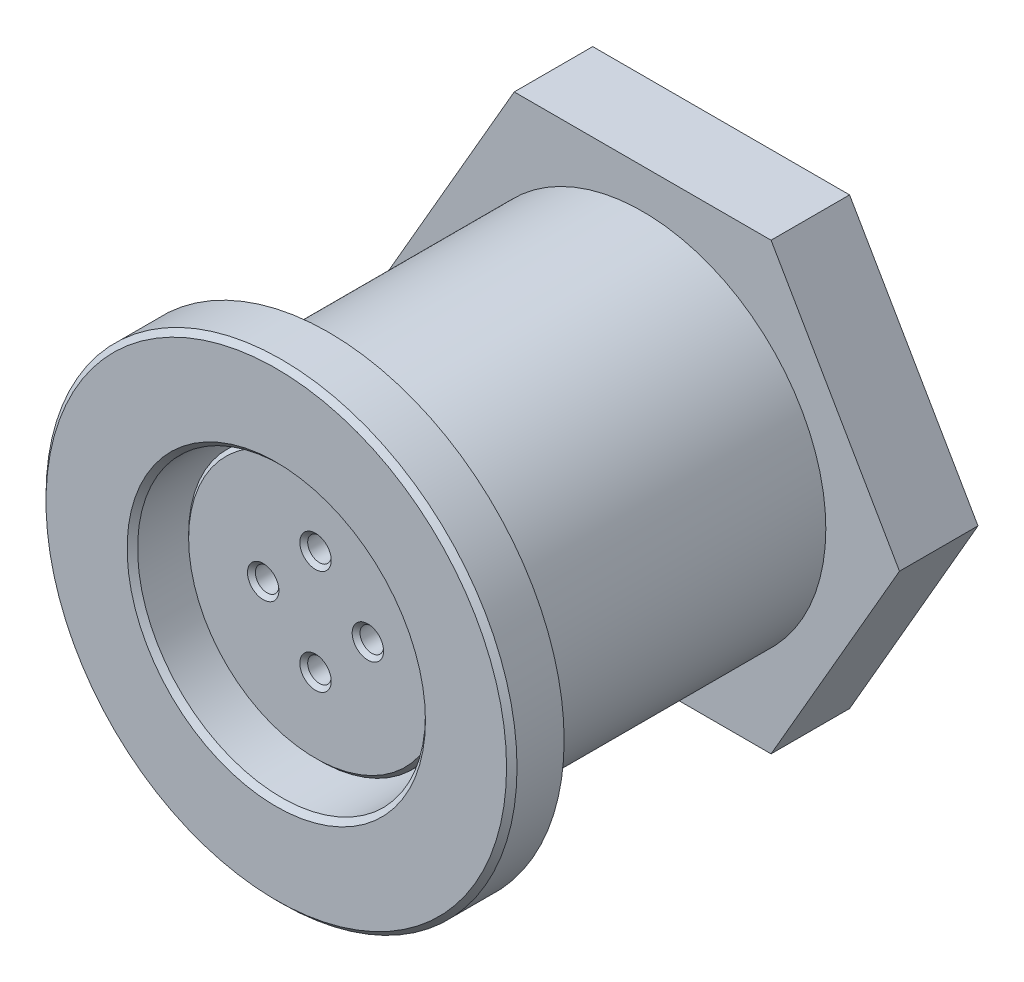
SolidWorks part; units mm, degrees
material "1060 Alloy"
ref_plane "Front Plane" through (0, 0, 0) normal (0, 0, 1) x (1, 0, 0)
ref_plane "Top Plane" through (0, 0, 0) normal (0, 1, 0) x (1, 0, 0)
ref_plane "Right Plane" through (0, 0, 0) normal (1, 0, 0) x (0, 0, -1)
sketch "Sketch1" plane through (0, 0, 0) normal (0, 0, 1) x (1, 0, 0)
  circle A0 centre (0, 0) radius 9
extrude "Extrude1" add sketch "Sketch1" along normal blind 2
sketch "Sketch3" plane through (0, 0, 0) normal (0, 0, -1) x (-1, 0, 0)
  circle A0 centre (0, 0) radius 8.25
  circle A1 centre (0, 0) radius 7
sketch "Sketch4" plane through (0, 0, 0) normal (0, 0, -1) x (-1, 0, 0)
  circle A0 centre (0, 0) radius 7
extrude "Extrude2" add sketch "Sketch4" along normal blind 16
sketch "Sketch2" plane through (0, 0, 2) normal (0, 0, 1) x (1, 0, 0)
  circle A0 centre (0, 0) radius 5.5
extrude "Cut-Extrude1" cut sketch "Sketch2" against normal blind 10
extrude "Cut-Extrude2" cut sketch "Sketch3" against normal blind 1
sketch "Sketch5" plane through (0, 0, -8) normal (0, 0, 1) x (1, 0, 0)
  circle A0 centre (0, 0) radius 5
extrude "Extrude3" add sketch "Sketch5" along normal blind 8.5
sketch "Sketch6" plane through (0, 0, 0.5) normal (0, 0, 1) x (1, 0, 0)
  circle A0 centre (0, 2) radius 0.45
  circle A1 centre (0, -2) radius 0.45
  circle A2 centre (2, 0) radius 0.45
  circle A3 centre (-2, 0) radius 0.45
  dimension "D1" = 2
  dimension "D2" = 2
  dimension "D3" = 2
  dimension "D4" = 2
extrude "Cut-Extrude3" cut sketch "Sketch6" against normal blind 7
chamfer "Chamfer2" distance 0.15 angle 45 5 edges at (5, 0, 0.5) (0.45, -2, 0.5) (0.45, 2, 0.5) (2.45, 0, 0.5) (-1.55, 0, 0.5)
chamfer "Chamfer1" distance 0.2 angle 45 2 edges at (9, 0, 2) (5.5, 0, 2)
sketch "Sketch7" plane through (0, 0, -16) normal (0, 0, -1) x (-1, 0, 0)
  circle A0 centre (0, 0) radius 5.5
extrude "Cut-Extrude4" cut sketch "Sketch7" against normal blind 1
chamfer "Chamfer3" distance 0.5 angle 45 1 edges at (-7, 0, -16)
sketch "Sketch8" plane through (0, 0, -15) normal (0, 0, -1) x (-1, 0, 0)
  line L0 (-4.9075, 8.5) -> (4.9075, 8.5)
  line L1 (4.9075, 8.5) -> (9.815, 0)
  line L2 (9.815, 0) -> (4.9075, -8.5)
  line L3 (4.9075, -8.5) -> (-4.9075, -8.5)
  line L4 (-4.9075, -8.5) -> (-9.815, 0)
  line L5 (-9.815, 0) -> (-4.9075, 8.5)
  line L6 (0, 8.5) -> (0, -8.5) construction
  dimension "D1" = 17
  dimension "D2" = 17
extrude "Extrude4" add sketch "Sketch8" against normal blind 3
